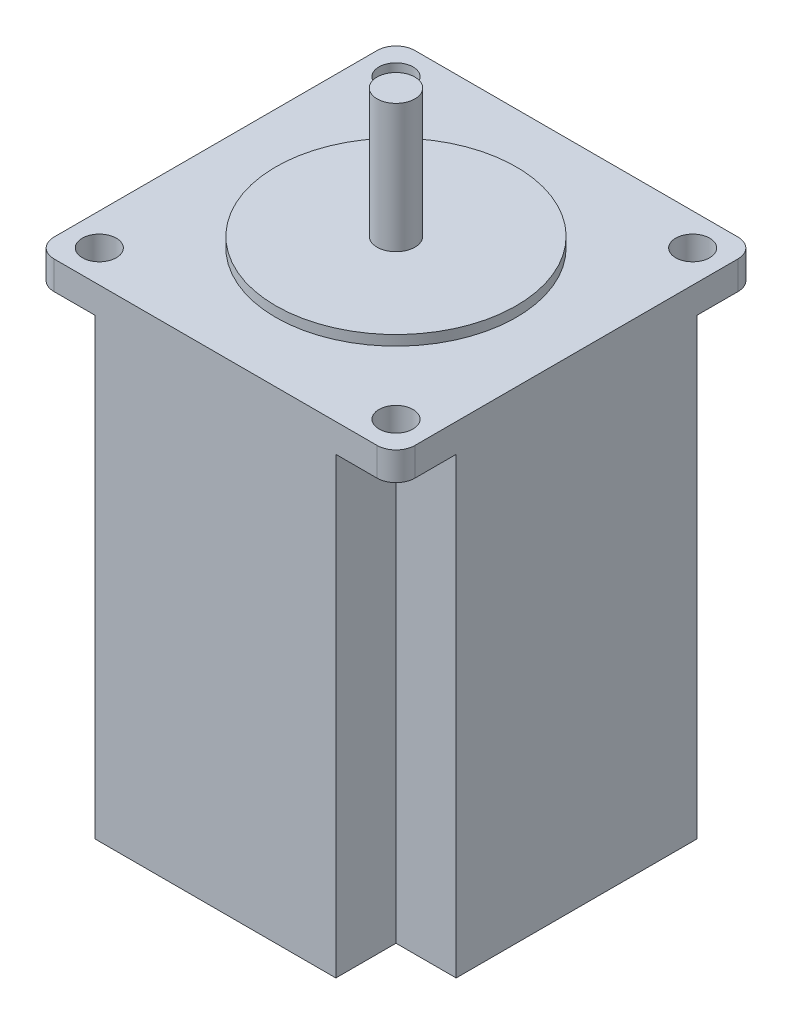
SolidWorks part; units mm, degrees
ref_plane "Front Plane" through (0, 0, 0) normal (0, 0, 1) x (1, 0, 0)
ref_plane "Top Plane" through (0, 0, 0) normal (0, 1, 0) x (1, 0, 0)
ref_plane "Right Plane" through (0, 0, 0) normal (1, 0, 0) x (0, 0, -1)
sketch "Sketch1" plane through (0, 0, 0) normal (0, 1, 0) x (1, 0, 0)
  line L1 (-28.65, 28.65) -> (28.65, 28.65)
  line L2 (-28.65, 28.65) -> (-28.65, -28.65)
  line L3 (-28.65, -28.65) -> (28.65, -28.65)
  line L4 (28.65, 28.65) -> (28.65, -28.65)
  line L5 (-28.65, 28.65) -> (28.65, -28.65) construction
  line L6 (-28.65, -28.65) -> (28.65, 28.65) construction
  point P0 (0, 0)
  dimension "D1" = 57.3
extrude "Boss-Extrude1" add sketch "Sketch1" along normal blind 76.5 contours L1 L4 L3 L2
sketch "Sketch2" plane through (0, 0, 0) normal (0, -1, 0) x (1, 0, 0)
  line L0 (-28.65, 28.65) -> (-19.1, 28.65)
  line L1 (-28.65, 28.65) -> (28.65, 28.65) construction
  line L2 (-19.1, 28.65) -> (-19.1, 19.1)
  line L3 (-19.1, 19.1) -> (-28.65, 19.1)
  line L5 (-28.65, 19.1) -> (-28.65, 28.65)
  dimension "D1" = 9.55
  dimension "D2" = 9.55
  dimension "D3" = 9.55
extrude "Cut-Extrude1" cut sketch "Sketch2" against normal blind 72
mirror "Mirror1" about plane through (0, 0, 0) normal (1, 0, 0) of "Cut-Extrude1"
mirror "Mirror2" about plane through (0, 0, 0) normal (0, 0, 1) of "Mirror1", "Cut-Extrude1"
sketch "Sketch3" plane through (0, 76.5, 0) normal (0, 1, 0) x (1, 0, 0)
  circle A0 centre (0, 0) radius 19.1
  dimension "D1" = 38.2
extrude "Boss-Extrude2" add sketch "Sketch3" along normal blind 1.6 contours A0
sketch "Sketch4" plane through (0, 78.1, 0) normal (0, 1, 0) x (1, 0, 0)
  circle A0 centre (0, 0) radius 3
  dimension "D1" = 6
extrude "Boss-Extrude3" add sketch "Sketch4" along normal blind 20.4 contours A0
sketch "Sketch5" plane through (0, 76.5, 0) normal (0, 1, 0) x (1, 0, 0)
  line L1 (-28.65, 28.65) -> (-28.65, -28.65) construction
  line L2 (-28.65, 28.65) -> (28.65, 28.65) construction
  line L3 (28.65, 28.65) -> (28.65, -28.65) construction
  line L4 (-28.65, -28.65) -> (28.65, -28.65) construction
  circle A0 centre (-23.55, 23.55) radius 2.7
  circle A1 centre (23.55, 23.55) radius 2.7
  circle A2 centre (23.55, -23.55) radius 2.7
  circle A3 centre (-23.55, -23.55) radius 2.7
  dimension "D1" = 5.4
  dimension "D2" = 5.4
  dimension "D3" = 5.4
  dimension "D4" = 5.4
  dimension "D5" = 47.1
  dimension "D6" = 47.1
  dimension "D7" = 47.1
  dimension "D8" = 47.1
  dimension "D9" = 5.1
  dimension "D10" = 5.1
  dimension "D11" = 5.1
  dimension "D12" = 5.1
  dimension "D13" = 5.1
  dimension "D14" = 5.1
  dimension "D15" = 5.1
  dimension "D16" = 5.1
extrude "Cut-Extrude2" cut sketch "Sketch5" against normal up to surface (4.5 mm away) up to face at (23.875, 72, -23.875)
fillet "Fillet2" radius 3 4 edges at (28.65, 74.25, 28.65) (28.65, 74.25, -28.65) (-28.65, 74.25, 28.65) (-28.65, 74.25, -28.65)
sketch "Sketch6" plane through (-28.65, 0, 0) normal (-1, 0, 0) x (0, 0, 1)
  line L0 (0, 0) -> (5.45, 0)
  line L1 (-19.1, 0) -> (19.1, 0) construction
  line L2 (0, 0) -> (-5.45, 0)
  line L3 (-5.45, 0) -> (-5.45, 9.6)
  line L4 (-5.45, 9.6) -> (5.45, 9.6)
  line L5 (5.45, 9.6) -> (5.45, 0)
  dimension "D1" = 5.45
  dimension "D2" = 5.45
  dimension "D3" = 9.6
  dimension "D4" = 10.9
extrude "Boss-Extrude4" add sketch "Sketch6" along normal blind 1.6
sketch "Sketch7" plane through (-30.25, 0, 0) normal (-1, 0, 0) x (0, 0, 1)
  line L0 (0, 0) -> (-4, 0)
  line L1 (-5.45, 0) -> (5.45, 0) construction
  line L2 (0, 0) -> (4, 0)
  line L3 (4, 0) -> (4, 2)
  line L4 (4, 2) -> (-4, 2)
  line L5 (-4, 2) -> (-4, 0)
  dimension "D1" = 4
  dimension "D2" = 4
  dimension "D3" = 2
  dimension "D4" = 8
extrude "Boss-Extrude5" add sketch "Sketch7" along normal blind 5.1
sketch "Sketch8" plane through (0, 0, 0) normal (0, -1, 0) x (1, 0, 0)
  line L0 (-28.65, -5.45) -> (-28.65, 5.45)
sketch "Sketch9" plane through (0, 0, 0) normal (0, -1, 0) x (1, 0, 0)
  circle A0 centre (0, 0) radius 3
  dimension "D1" = 6
extrude "Cut-Extrude3" cut sketch "Sketch9" against normal blind 5.1
